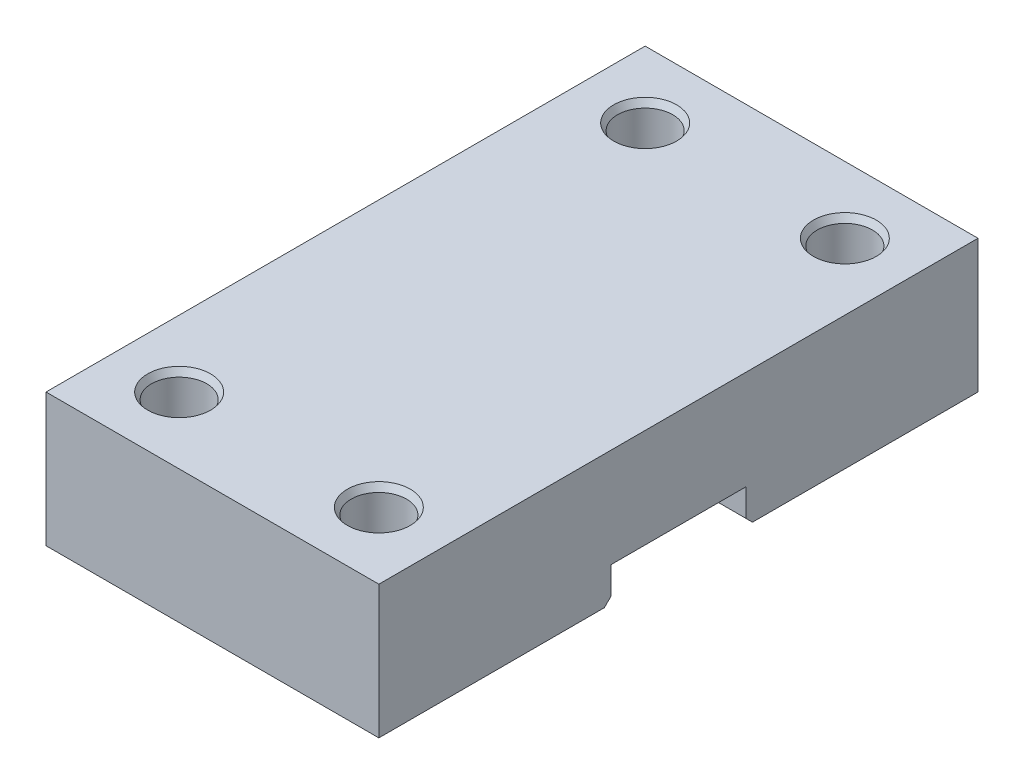
SolidWorks part; units mm, degrees
ref_plane "Спереди" through (0, 0, 0) normal (0, 0, 1) x (1, 0, 0)
ref_plane "Сверху" through (0, 0, 0) normal (0, 1, 0) x (1, 0, 0)
ref_plane "Справа" through (0, 0, 0) normal (1, 0, 0) x (0, 0, -1)
sketch "Sketch1" plane through (0, 0, 0) normal (0, 1, 0) x (1, 0, 0)
  line L1 (25, -45) -> (-25, -45)
  line L2 (25, -45) -> (25, 45)
  line L3 (25, 45) -> (-25, 45)
  line L4 (-25, -45) -> (-25, 45)
  line L5 (25, -45) -> (-25, 45) construction
  line L6 (25, 45) -> (-25, -45) construction
  point P0 (0, 0)
  dimension "D1" = 50
  dimension "D2" = 90
extrude "Boss-Extrude1" add sketch "Sketch1" along normal blind 20
sketch "Sketch2" plane through (25, 0, 0) normal (1, 0, 0) x (0, 0, -1)
  line L0 (0, 0) -> (0, 20) construction
  line L1 (-45, 0) -> (45, 0) construction
  line L2 (-45, 20) -> (45, 20) construction
  line L4 (10.125, 5.1) -> (-10.125, 5.1)
  line L5 (10.125, 5.1) -> (10.125, 0)
  line L6 (10.125, 0) -> (-10.125, 0)
  line L7 (-10.125, 5.1) -> (-10.125, 0)
  line L8 (10.125, 5.1) -> (-10.125, 0) construction
  line L9 (10.125, 0) -> (-10.125, 5.1) construction
  point P6 (0, 2.55)
  dimension "D1" = 20.25
  dimension "D2" = 5.1
extrude "Cut-Extrude1" cut sketch "Sketch2" against normal through all and the other way through all
sketch "Sketch3" plane through (0, 0, 0) normal (0, -1, 0) x (1, 0, 0)
  line L0 (-15, 35) -> (15, -35) construction
  line L1 (-15, -35) -> (15, 35) construction
  line L2 (0, 45) -> (0, -45) construction
  line L3 (25, 35) -> (-25, 35) construction
  line L4 (25, 45) -> (25, 10.125) construction
  line L5 (-25, 10.125) -> (-25, 45) construction
  line L6 (-25, -35) -> (25, -35) construction
  line L7 (-25, -45) -> (-25, -10.125) construction
  line L8 (25, -10.125) -> (25, -45) construction
  line L9 (-25, 45) -> (25, 45) construction
  line L10 (25, -45) -> (-25, -45) construction
  circle A0 centre (-15, 35) radius 4.15
  circle A1 centre (-15, -35) radius 4.15
  circle A2 centre (15, 35) radius 4.15
  circle A3 centre (15, -35) radius 4.15
  point P6 (0, 0)
  point P7 (0, 0)
  dimension "D1" = 8.3
  dimension "D2" = 30
  dimension "D3" = 70
extrude "Cut-Extrude2" cut sketch "Sketch3" against normal through all
chamfer "Chamfer1" distance 1 angle 30 4 edges at (-15, 20, -39.15) (15, 20, -39.15) (15, 20, 30.85) (-15, 20, 30.85)
chamfer "Chamfer2" distance 1 angle 45 2 edges at (0, 0, -10.125) (0, 0, 10.125)
